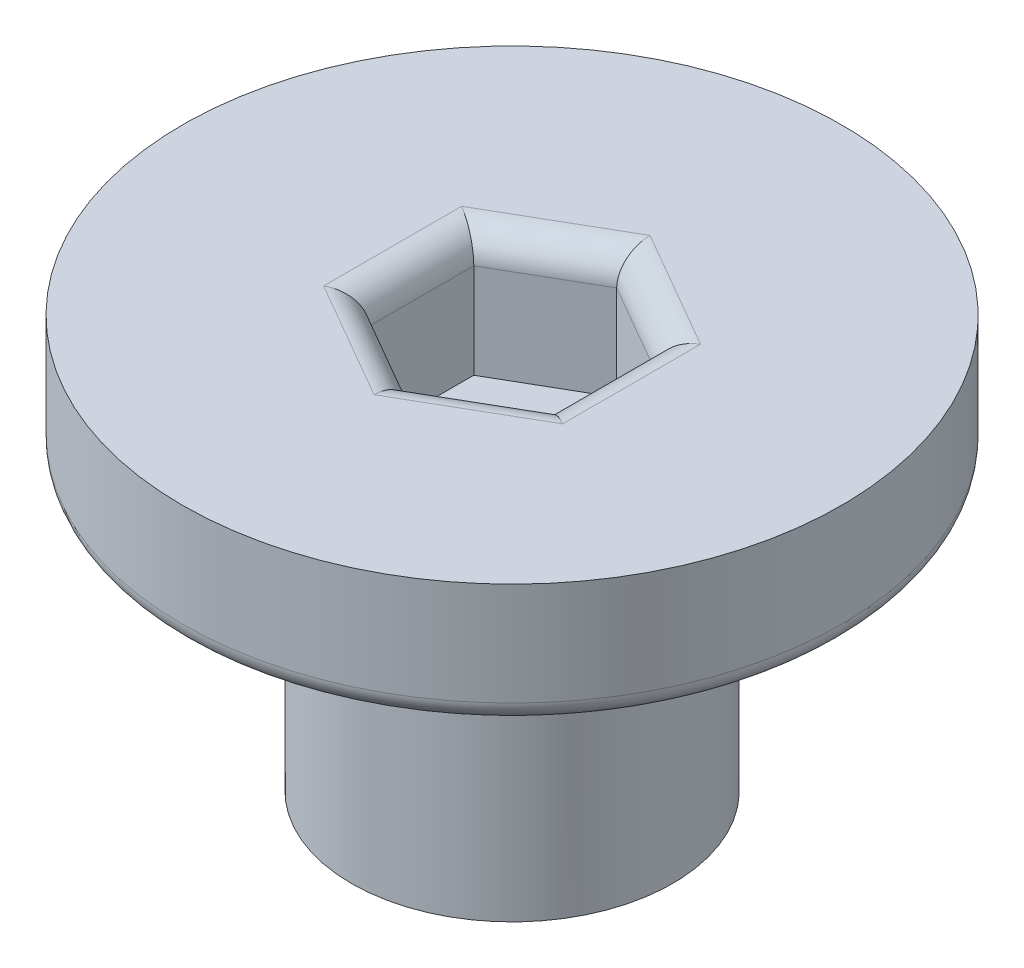
SolidWorks part; units mm, degrees
ref_plane "Front Plane" through (0, 0, 0) normal (0, 0, 1) x (1, 0, 0)
ref_plane "Top Plane" through (0, 0, 0) normal (0, 1, 0) x (1, 0, 0)
ref_plane "Right Plane" through (0, 0, 0) normal (1, 0, 0) x (0, 0, -1)
sketch "Sketch1" plane through (0, 0, 0) normal (0, 1, 0) x (1, 0, 0)
  circle A0 centre (0, 0) radius 8
  dimension "D1" = 16
extrude "Boss-Extrude1" add sketch "Sketch1" along normal blind 3
sketch "Sketch2" plane through (0, 0, 0) normal (0, -1, 0) x (1, 0, 0)
  circle A0 centre (0, 0) radius 3.9
  dimension "D1" = 7.8
extrude "Boss-Extrude2" add sketch "Sketch2" along normal blind 7
sketch "Sketch3" plane through (0, -7, 0) normal (0, -1, 0) x (1, 0, 0)
  circle A0 centre (0, 0) radius 1.15
  dimension "D1" = 2.3
extrude "Cut-Extrude3" cut sketch "Sketch3" against normal blind 12
sketch "Sketch6" plane through (0, 3, 0) normal (0, 1, 0) x (1, 0, 0)
  line L7 (0, 2.5403) -> (-2.2, 1.2702)
  line L8 (-2.2, 1.2702) -> (-2.2, -1.2702)
  line L9 (-2.2, -1.2702) -> (0, -2.5403)
  line L10 (0, -2.5403) -> (2.2, -1.2702)
  line L11 (2.2, -1.2702) -> (2.2, 1.2702)
  line L12 (2.2, 1.2702) -> (0, 2.5403)
  circle A0 centre (0, 0) radius 2.2 construction
extrude "Cut-Extrude4" cut sketch "Sketch6" against normal blind 3
fillet "Fillet1" radius 0.7 6 edges at (2.2, 3, 0) (1.1, 3, 1.9053) (-1.1, 3, 1.9053) (-2.2, 3, 0) (-1.1, 3, -1.9053) (1.1, 3, -1.9053)
fillet "Fillet2" radius 0.5 1 edges at (0, -7, -1.15)
fillet "Fillet3" radius 0.5 2 edges at (0, 0, 8) (0, 0, -3.9)
